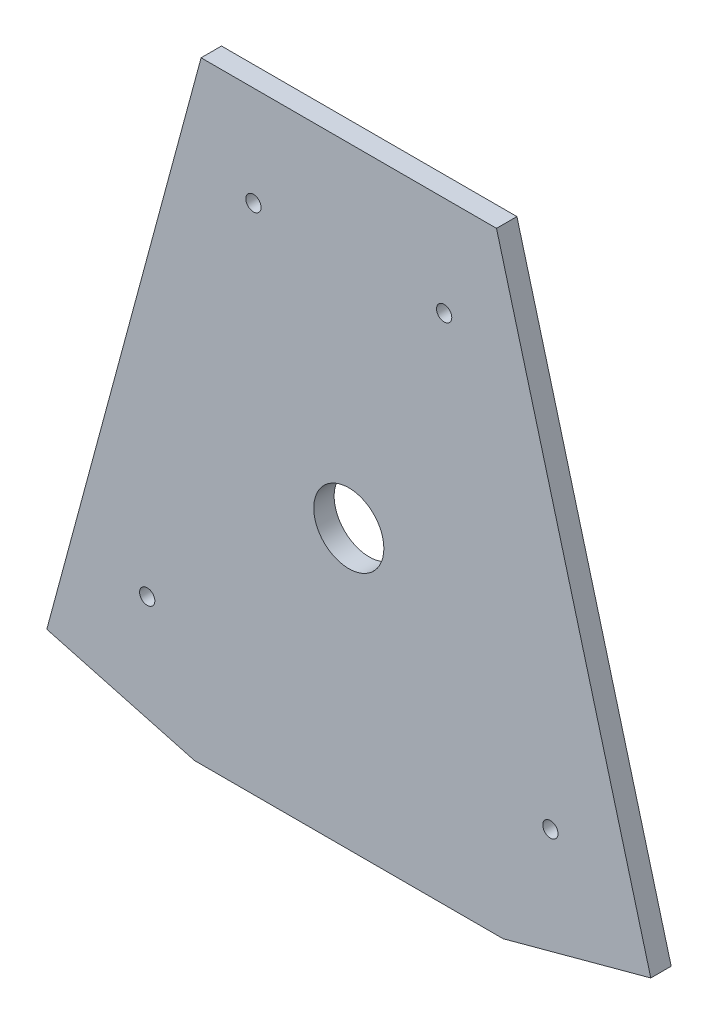
SolidWorks part; units mm, degrees
ref_plane "Front Plane" through (0, 0, 0) normal (0, 0, 1) x (1, 0, 0)
ref_plane "Top Plane" through (0, 0, 0) normal (0, 1, 0) x (1, 0, 0)
ref_plane "Right Plane" through (0, 0, 0) normal (1, 0, 0) x (0, 0, -1)
sketch "Sketch1" plane through (0, 0, 0) normal (0, 0, 1) x (1, 0, 0)
  line L0 (-36.7856, 9.9211) -> (0, 0) construction
  line L1 (0, 0) -> (36.7856, 9.9211) construction
  line L2 (-18.3928, 4.9606) -> (-335.8693, -1172.1789) construction
  line L3 (-335.8693, -1172.1789) -> (-355.6, -1172.1789) construction
  line L4 (-36.7856, 9.9211) -> (36.7856, 9.9211)
  line L5 (36.7856, 9.9211) -> (75.2124, -132.5577)
  line L6 (75.2124, -132.5577) -> (38.4268, -142.4789)
  line L7 (38.4268, -142.4789) -> (-38.4268, -142.4789)
  line L8 (-38.4268, -142.4789) -> (-75.2124, -132.5577)
  line L9 (-75.2124, -132.5577) -> (-36.7856, 9.9211)
  line L10 (-38.4268, -142.4789) -> (0, 0) construction
  dimension "D2" = 38.1
  dimension "D3" = 355.6
  dimension "D4" = 1219.2
  dimension "D5" = 152.4
extrude "Boss-Extrude1" add sketch "Sketch1" along normal blind 5.08
sketch "Sketch2" plane through (0, 0, 5.08) normal (0, 0, 1) x (1, 0, 0)
  line L0 (-36.5125, -73.1574) -> (36.5125, -73.1574) construction
  line L1 (-38.4268, -142.4789) -> (-18.3928, -68.1968) construction
  line L2 (-36.7856, 9.9211) -> (-75.2124, -132.5577) construction
  line L3 (18.3928, -68.1968) -> (38.4268, -142.4789) construction
  circle A0 centre (0, -73.1574) radius 19.05
  circle A1 centre (-36.5125, -73.1574) radius 5.5562
  circle A2 centre (36.5125, -73.1574) radius 5.5562
  dimension "D1" = 38.1
  dimension "D3" = 11.1125
  dimension "D2" = 73.025
extrude "Cut-Extrude1" cut sketch "Sketch2" against normal through all
hole_wizard "#6 Clearance Hole1" positions "Sketch3" profile "Sketch4" hole size "#6" standard "ANSI Inch" end condition through all
sketch "Sketch3" plane through (0, 0, 5.08) normal (0, 0, 1) x (1, 0, 0)
  line L17 (-56.8196, -137.5183) -> (-17.0549, 9.9211)
  line L18 (-75.2124, -132.5577) -> (-38.4268, -142.4789) construction
  line L19 (36.7856, 9.9211) -> (-36.7856, 9.9211) construction
  line L21 (17.0549, 9.9211) -> (56.8196, -137.5183)
  line L22 (38.4268, -142.4789) -> (75.2124, -132.5577) construction
  line L24 (75.2124, -132.5577) -> (36.7856, 9.9211) construction
  line L25 (-36.7856, 9.9211) -> (-75.2124, -132.5577) construction
  point P75 (-50.2055, -112.9945)
  point P77 (-23.7491, -14.8996)
  point P80 (23.7491, -14.8996)
  point P82 (50.2055, -112.9945)
  dimension "D1" = 25.4
  dimension "D2" = 101.6
sketch "Sketch4" plane through (50.2055, -112.9945, 5.08) normal (1, 0, 0) x (0, -1, 0)
  line L0 (0, 0) -> (0, 5.08)
  line L1 (0, 5.08) -> (1.8986, 5.08)
  line L2 (1.8986, 5.08) -> (1.8986, 0)
  line L5 (1.8986, 0) -> (0, 0)
  line L11 (0, -6.35) -> (0, 107.95) construction
  dimension "Thru Hole Dia." = 3.7973
  dimension "Thru Hole Depth" = 5.08
sketch "Sketch5" plane through (0, 0, 5.08) normal (0, 0, 1) x (1, 0, 0)
  circle A0 centre (0, -73.1574) radius 19.05 construction
  circle A1 centre (36.5125, -73.1574) radius 5.5562 construction
  circle A2 centre (-36.5125, -73.1574) radius 5.5562 construction
  circle A3 centre (0, -73.1574) radius 19.05
  circle A4 centre (36.5125, -73.1574) radius 5.5562
  circle A5 centre (-36.5125, -73.1574) radius 5.5562
  circle A6 centre (0, -73.1574) radius 8.7313
  dimension "D1" = 17.4625
extrude "Boss-Extrude2" add sketch "Sketch5" against normal up to surface (5.08 mm away) up to face at (-48.3069, -112.9945, 0)
